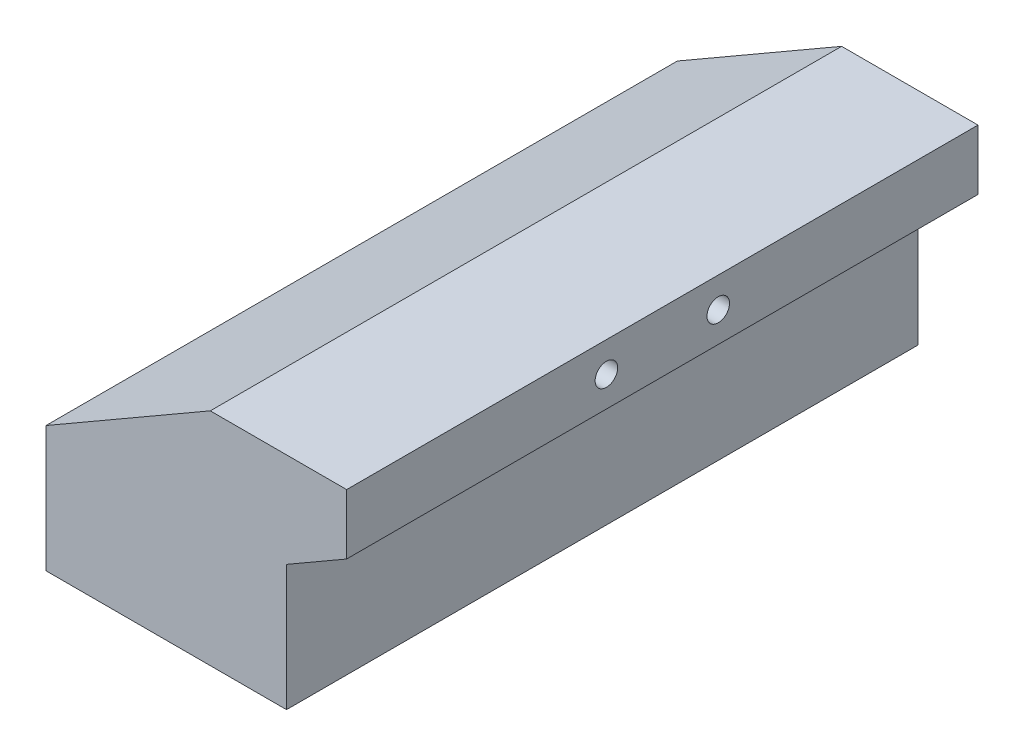
SolidWorks part; units mm, degrees
ref_plane "Front Plane" through (0, 0, 0) normal (0, 0, 1) x (1, 0, 0)
ref_plane "Top Plane" through (0, 0, 0) normal (0, 1, 0) x (1, 0, 0)
ref_plane "Right Plane" through (0, 0, 0) normal (1, 0, 0) x (0, 0, -1)
sketch "Sketch1" plane through (0, 0, 0) normal (0, 0, 1) x (1, 0, 0)
  line L0 (0, 26.5767) -> (34.697, 46.609)
  line L1 (0, 0) -> (50.8, 0)
  line L2 (0, 0) -> (0, 26.5767)
  line L3 (0, 26.5767) -> (50.8, 26.5767)
  line L4 (50.8, 0) -> (50.8, 26.5767)
  line L5 (34.697, 46.609) -> (63.5, 46.609)
  line L6 (63.5, 46.609) -> (63.5, 33.909)
  line L7 (63.5, 33.909) -> (50.8, 26.5767)
  line L8 (63.5, 40.259) -> (23.6985, 40.259) construction
  point P5 (63.5, 40.259)
  dimension "D1" = 30
  dimension "D2" = 40.259
  dimension "D3" = 12.7
  dimension "D4" = 50.8
  dimension "D5" = 12.7
extrude "Boss-Extrude1" add sketch "Sketch1" along normal mid plane 133.35 contours L1 L4 L3 L2 | L6 L8 L0 L3 L7 | L8 L6 L5 L0
shell "Shell1" [suppressed] thickness 3.175
sketch "Sketch3" plane through (63.5, 0, 0) normal (1, 0, 0) x (0, 0, -1)
  line L0 (-66.675, 46.609) -> (66.675, 33.909) construction
  line L1 (-66.675, 33.909) -> (66.675, 46.609) construction
  line L2 (0, 40.259) -> (-66.675, 40.259) construction
  line L3 (0, 40.259) -> (66.675, 40.259) construction
  line L4 (-66.675, 46.609) -> (-66.675, 33.909) construction
  line L5 (66.675, 46.609) -> (66.675, 33.909) construction
  circle A0 centre (-11.811, 40.259) radius 2.3812
  circle A1 centre (11.811, 40.259) radius 2.3813
  dimension "D3" = 4.7625
  dimension "D1" = 23.622
  dimension "D2" = 11.811
extrude "Cut-Extrude1" cut sketch "Sketch3" against normal blind 9.525
